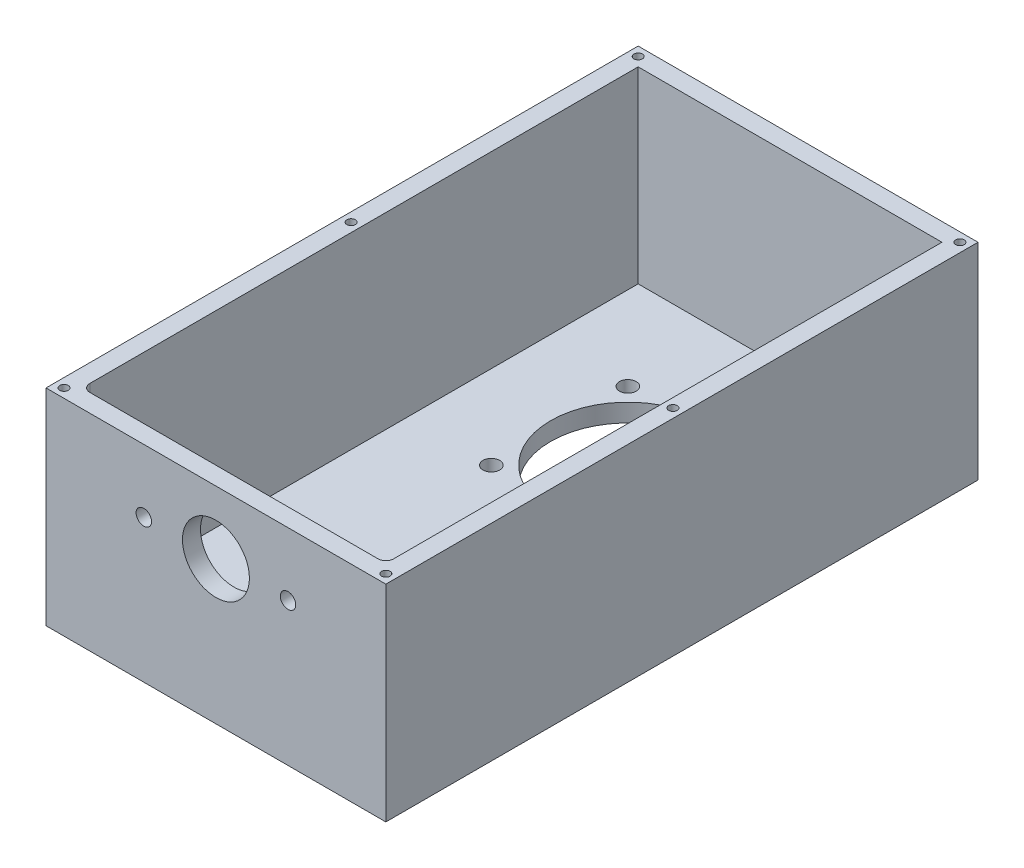
SolidWorks part; units mm, degrees
material "1060 合金"
ref_plane "前视基准面" through (0, 0, 0) normal (0, 0, 1) x (1, 0, 0)
ref_plane "上视基准面" through (0, 0, 0) normal (0, 1, 0) x (1, 0, 0)
ref_plane "右视基准面" through (0, 0, 0) normal (1, 0, 0) x (0, 0, -1)
sketch "草图1" plane through (0, 0, 0) normal (0, 0, 1) x (1, 0, 0)
  line L1 (-66, -40) -> (66, -40)
  line L2 (-66, -40) -> (-66, 40)
  line L3 (-66, 40) -> (66, 40)
  line L4 (66, -40) -> (66, 40)
  line L5 (-66, -40) -> (66, 40) construction
  line L6 (-66, 40) -> (66, -40) construction
  point P0 (0, 0)
  dimension "D1" = 132
  dimension "D2" = 80
extrude "凸台-拉伸1" add sketch "草图1" against normal blind 230
sketch "草图2" plane through (0, 40, 0) normal (0, 1, 0) x (1, 0, 0)
  line L0 (-59, 7) -> (59, 7)
  line L1 (-59, 7) -> (-59, 223)
  line L2 (59, 7) -> (59, 223)
  line L3 (-59, 223) -> (59, 223)
  line L4 (66, 230) -> (-66, 230) construction
  line L5 (0, 0) -> (0, 70.9714) construction
  line L6 (-66, 230) -> (-66, 0) construction
  line L8 (66, 0) -> (-66, 0) construction
  point P11 (59.2947, 211.8639)
  point P13 (116.7645, 217.0884)
  dimension "D1" = 7
  dimension "D2" = 7
  dimension "D3" = 7
extrude "切除-拉伸1" cut sketch "草图2" against normal blind 73
sketch "草图3" plane through (0, 0, 0) normal (0, 0, 1) x (1, 0, 0)
  line L0 (0, -40) -> (0, 40) construction
  line L1 (0, 15.5) -> (-61.797, 15.5) construction
  line L2 (0, 15.5) -> (28, 15.5) construction
  line L3 (-66, -40) -> (66, -40) construction
  line L4 (66, 40) -> (-66, 40) construction
  circle A0 centre (0, 15.5) radius 13
  circle A1 centre (-28, 15.5) radius 3
  circle A2 centre (28, 15.5) radius 3
  dimension "D1" = 26
  dimension "D2" = 6
  dimension "D3" = 28
  dimension "D4" = 24.5
extrude "切除-拉伸2" cut sketch "草图3" against normal blind 10
sketch "草图4" plane through (0, -33, 0) normal (0, 1, 0) x (1, 0, 0)
  line L0 (0, 160) -> (26.5165, 186.5165) construction
  line L1 (0, 160) -> (48.6437, 160) construction
  line L2 (0, 230) -> (0, 135.1289) construction
  line L3 (59, 230) -> (-59, 230) construction
  line L4 (0, 160) -> (0, 219.8731) construction
  circle A0 centre (26.5165, 186.5165) radius 3.25
  circle A1 centre (26.5165, 133.4835) radius 3.25
  circle A2 centre (-26.5165, 133.4835) radius 3.25
  circle A3 centre (-26.5165, 186.5165) radius 3.25
  circle A4 centre (0, 160) radius 30
  dimension "D3" = 6.5
  dimension "D4" = 60
  dimension "D1" = 45
  dimension "D2" = 37.5
  dimension "D5" = 70
  dimension "D6" = 4
extrude "切除-拉伸3" cut sketch "草图4" against normal blind 10
fillet "圆角1" radius 3 2 edges at (59, 3.5, -7) (-59, 3.5, -7)
sketch "草图5" plane through (0, 40, 0) normal (0, 1, 0) x (1, 0, 0)
  line L0 (0, 0) -> (0, 223) construction
  line L1 (59, 223) -> (-59, 223) construction
  line L2 (66, 230) -> (-66, 230) construction
  line L3 (-66, 230) -> (-66, 0) construction
  line L4 (66, 0) -> (-66, 0) construction
  point P0 (-62.5, 226.5)
  point P1 (-62.5, 3.5)
  point P2 (-62.5, 115)
  point P17 (62.5, 115)
  point P18 (62.5, 3.5)
  point P19 (62.5, 226.5)
  point P20 (0, 0)
  dimension "D1" = 3.5
  dimension "D2" = 3.5
  dimension "D3" = 3.5
  dimension "D4" = 115
hole_wizard "M4 螺纹孔1" positions "3D草图1" profile "草图6" tap size "M4" standard "GB"
sketch3d "3D草图1"
  point P0 (-62.5, 40, -226.5)
  point P3 (-62.5, 40, -115)
  point P6 (62.5, 40, -115)
  point P9 (62.5, 40, -226.5)
  point P12 (62.5, 40, -3.5)
  point P15 (-62.5, 40, -3.5)
sketch "草图6" plane through (-62.5, 40, -226.5) normal (1, 0, 0) x (0, 0, 1)
  line L0 (0, 0) -> (0, 11.0914)
  line L1 (0, 11.0914) -> (1.65, 10.1)
  line L2 (1.65, 10.1) -> (1.65, 0)
  line L5 (1.65, 0) -> (0, 0)
  line L10 (0, 11.0914) -> (-1.65, 10.1) construction
  line L11 (0, -6.35) -> (0, 107.95) construction
  dimension "螺纹孔钻头直径" = 3.3
  dimension "螺纹孔钻头深度" = 10.1
  dimension "导头角度" = 118
cosmetic thread "孔螺蚊线1" parameters "D1"=8, "D2"=4
cosmetic thread "孔螺蚊线2" parameters "D1"=8, "D2"=4
cosmetic thread "孔螺蚊线3" parameters "D1"=8, "D2"=4
cosmetic thread "孔螺蚊线4" parameters "D1"=8, "D2"=4
cosmetic thread "孔螺蚊线5" parameters "D1"=8, "D2"=4
cosmetic thread "孔螺蚊线6" parameters "D1"=8, "D2"=4
equation "\"3。5\"=4.83134"
